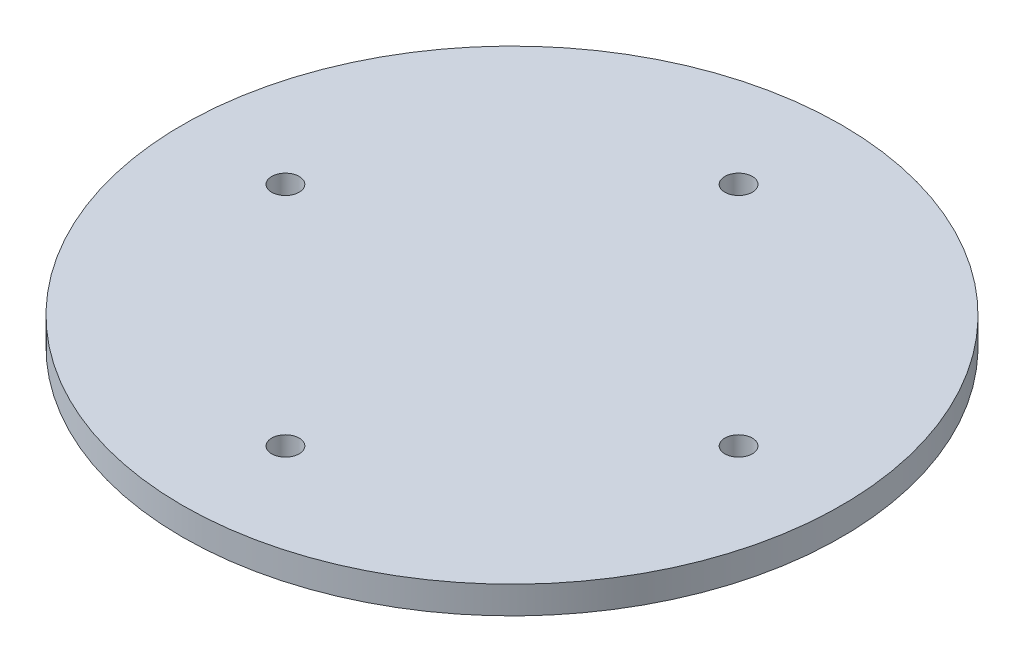
SolidWorks part; units mm, degrees
ref_plane "Front Plane" through (0, 0, 0) normal (0, 0, 1) x (1, 0, 0)
ref_plane "Top Plane" through (0, 0, 0) normal (0, 1, 0) x (1, 0, 0)
ref_plane "Right Plane" through (0, 0, 0) normal (1, 0, 0) x (0, 0, -1)
sketch "Sketch1" plane through (0, 0, 0) normal (0, 1, 0) x (1, 0, 0)
  line L0 (0, 0) -> (0, 58.5727) construction
  circle A0 centre (0, 0) radius 41.25 construction
  circle A1 centre (0, 41.25) radius 2.5
  circle A2 centre (41.25, 0) radius 2.5
  circle A3 centre (0, -41.25) radius 2.5
  circle A4 centre (-41.25, 0) radius 2.5
  circle A5 centre (0, 0) radius 60
  point P15 (0, 0)
  dimension "D1" = 82.5
  dimension "D2" = 5
  dimension "D4" = 120
  dimension "D3" = 4
extrude "Boss-Extrude1" add sketch "Sketch1" along normal blind 5
